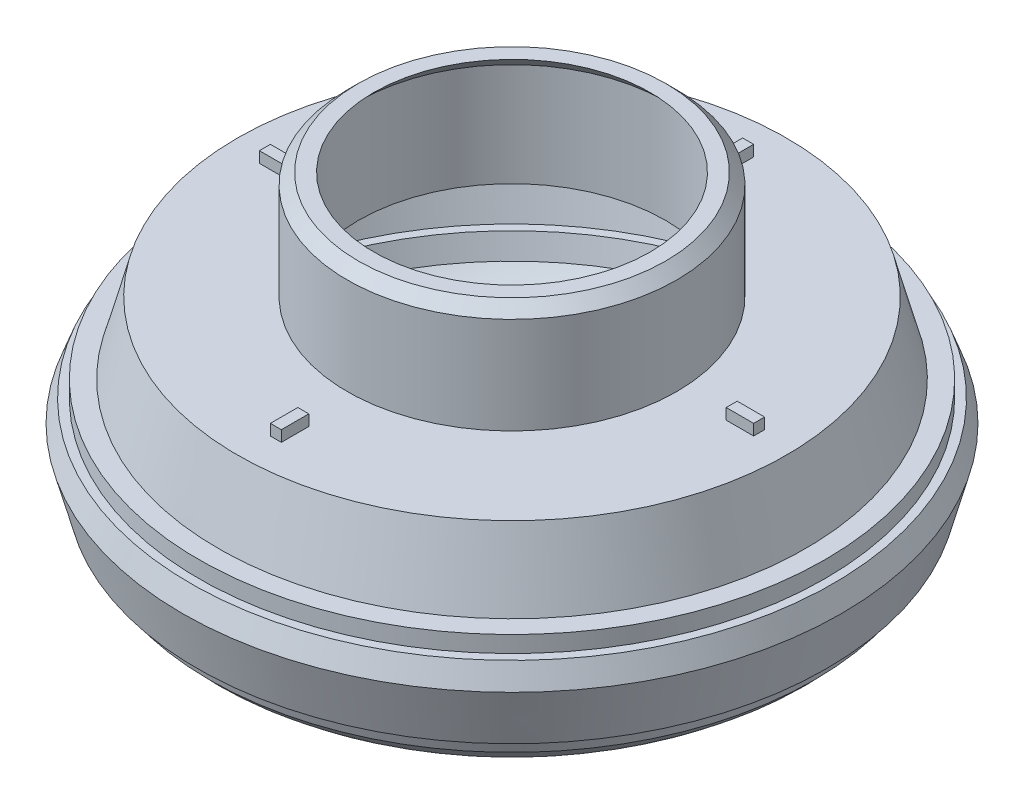
SolidWorks part; units mm, degrees
material "2024 Alloy"
ref_plane "Front Plane" through (0, 0, 0) normal (0, 0, 1) x (1, 0, 0)
ref_plane "Top Plane" through (0, 0, 0) normal (0, 1, 0) x (1, 0, 0)
ref_plane "Right Plane" through (0, 0, 0) normal (1, 0, 0) x (0, 0, -1)
sketch "Sketch1" plane through (0, 0, 0) normal (0, 0, 1) x (1, 0, 0)
  line L0 (-30, 0) -> (0, 0) construction
  line L4 (-25, 10) -> (-26.7417, 3.5)
  line L5 (-26.7417, 3.5) -> (-28.5, 3.5)
  line L6 (-28.5, 3.5) -> (-28.5, 2)
  line L7 (-28.5, 2) -> (-29.2583, 2)
  line L8 (-29.2583, 2) -> (-30, 0)
  line L15 (0, 10) -> (0, -10)
  line L20 (0, -10) -> (-19.9007, -10)
  line L21 (-30, 0) -> (-28.6603, -5)
  line L22 (-28.6603, -5) -> (-27.9019, -5)
  line L23 (-27.9019, -5) -> (-27.5, -6.5)
  line L24 (-25, 10) -> (0, 10)
  line L25 (0, 614.0197) -> (0, -539.7091) construction
  arc A4 (-27.5, -6.5) -> (-19.9007, -10) centre (-19.9007, 0) ccw
  point P2 (0, 0)
  dimension "D5" = 10
  dimension "D2" = 30
  dimension "D3" = 25
  dimension "D4" = 75
  dimension "D6" = 10
  dimension "D7" = 5
  dimension "D8" = 6.5
  dimension "D9" = 105
  dimension "D10" = 7
  dimension "D11" = 8
  dimension "D12" = 3.5
  dimension "D13" = 1.5
  dimension "D14" = 27.5
revolve "Revolve2" add sketch "Sketch1" angle 360 about L25
sketch "Sketch2" plane through (0, 10, 0) normal (0, 1, 0) x (1, 0, 0)
  circle A0 centre (0, 0) radius 15
  dimension "D1" = 30
extrude "Boss-Extrude1" add sketch "Sketch2" along normal blind 9.8
chamfer "Chamfer1" distance 1 angle 45 1 edges at (-15, 19.8, 0)
shell "Shell1" thickness 1
sketch "Sketch7" plane through (0, 10, 0) normal (0, 1, 0) x (1, 0, 0)
  line L0 (0, 0) -> (-22, 0) construction
  line L5 (-19.5, 0) -> (-22, 0)
  line L6 (-19.5, 0) -> (-19.5, -1)
  line L7 (-19.5, -1) -> (-22, -1)
  line L8 (-22, 0) -> (-22, -1)
  dimension "D1" = 1
  dimension "D2" = 2.5
  dimension "D3" = 22
extrude "Boss-Extrude5" add sketch "Sketch7" along normal blind 1
pattern_circular "CirPattern1" count 4 over 360 about axis through (0, 0, 0) along (0, 1, 0) of "Boss-Extrude5"
